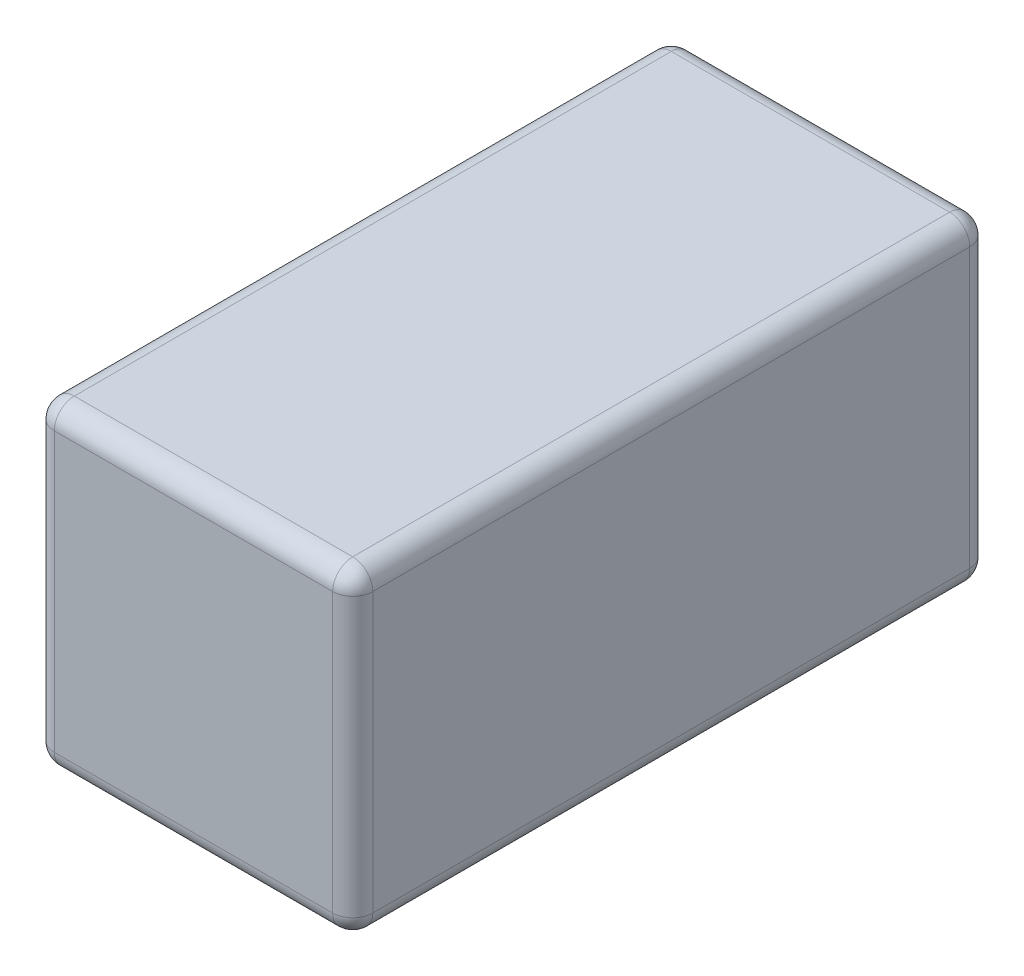
SolidWorks part; units mm, degrees
ref_plane "Front Plane" through (0, 0, 0) normal (0, 0, 1) x (1, 0, 0)
ref_plane "Top Plane" through (0, 0, 0) normal (0, 1, 0) x (1, 0, 0)
ref_plane "Right Plane" through (0, 0, 0) normal (1, 0, 0) x (0, 0, -1)
sketch "Sketch1" plane through (0, 0, 0) normal (0, 0, 1) x (1, 0, 0)
  line L1 (-0.7938, -0.7938) -> (0.7937, -0.7938)
  line L2 (-0.7938, -0.7938) -> (-0.7938, 0.7937)
  line L3 (-0.7938, 0.7937) -> (0.7937, 0.7937)
  line L4 (0.7937, -0.7938) -> (0.7937, 0.7937)
  line L5 (-0.7938, -0.7938) -> (0.7937, 0.7937) construction
  line L6 (-0.7938, 0.7937) -> (0.7937, -0.7938) construction
  point P0 (0, 0)
  dimension "D1" = 1.5875
  dimension "D2" = 1.5875
extrude "Boss-Extrude1" add sketch "Sketch1" along normal blind 3.175
fillet "Fillet1" radius 0.1 12 edges at (-0.7938, -0.7938, 1.5875) (0, -0.7938, 0) (0.7937, -0.7938, 1.5875) (0.7937, 0, 0) (0, -0.7938, 3.175) (-0.7938, 0, 3.175) (0.7937, 0, 3.175) (0.7937, 0.7937, 1.5875) (0, 0.7937, 3.175) (-0.7938, 0.7937, 1.5875) (0, 0.7937, 0) (-0.7938, 0, 0)
